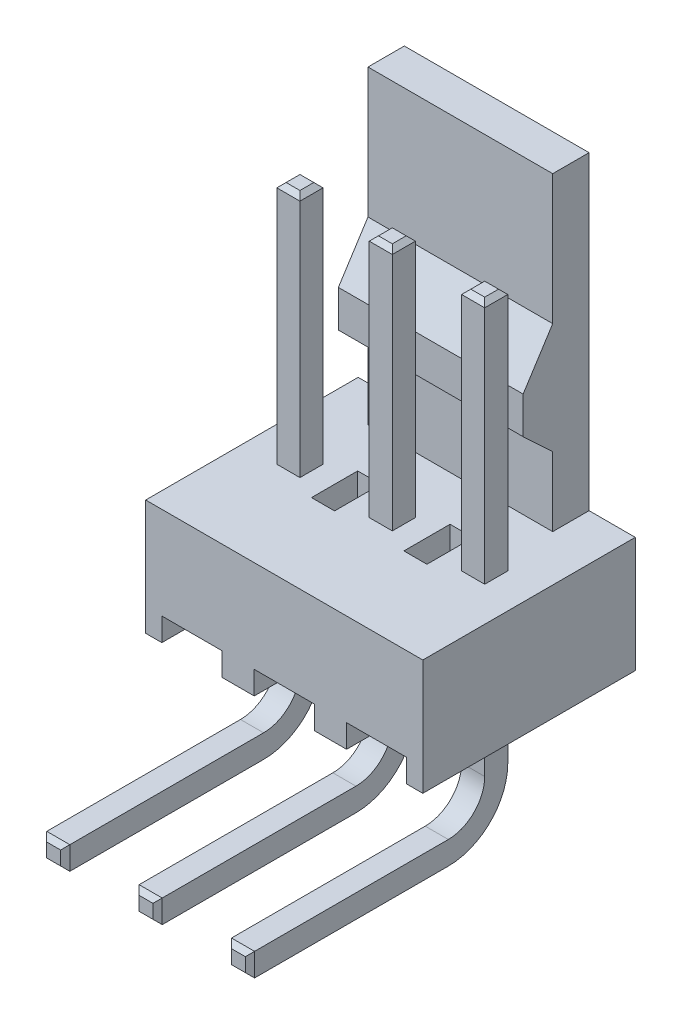
SolidWorks part; units mm, degrees
ref_plane "Front Plane" through (0, 0, 0) normal (0, 0, 1) x (1, 0, 0)
ref_plane "Top Plane" through (0, 0, 0) normal (0, 1, 0) x (1, 0, 0)
ref_plane "Right Plane" through (0, 0, 0) normal (1, 0, 0) x (0, 0, -1)
ref_plane "Plane1" through (0, -1.5875, 0) normal (0, -1, 0) x (1, 0, 0)
sketch "Sketch1" plane through (0, -1.5875, 0) normal (0, -1, 0) x (1, 0, 0)
  line L0 (-3.81, -2.8702) -> (2.54, -2.8702)
  line L1 (2.54, -2.8702) -> (2.54, 2.9718)
  line L2 (2.54, 2.9718) -> (-3.81, 2.9718)
  line L3 (-3.81, 2.9718) -> (-3.81, -2.8702)
extrude "Boss-Extrude1" add sketch "Sketch1" against normal blind 3.175
ref_plane "Plane2" through (2.54, 0, 0) normal (1, 0, 0) x (0, 0, -1)
sketch "Sketch2" plane through (2.54, 0, 0) normal (1, 0, 0) x (0, 0, -1)
  line L0 (0.651, 4.6355) -> (1.8702, 3.4925)
  line L1 (1.8702, 3.4925) -> (1.8702, 1.5875)
  line L2 (1.8702, 1.5875) -> (2.8702, 1.5875)
  line L3 (2.8702, 1.5875) -> (2.8702, 10.1125)
  line L4 (2.8702, 10.1125) -> (1.8702, 10.1125)
  line L5 (1.8702, 10.1125) -> (1.8702, 6.5405)
  line L6 (1.8702, 6.5405) -> (0.651, 4.6355)
extrude "Boss-Extrude2" add sketch "Sketch2" against normal blind 5.08
sketch "Sketch3" plane through (2.54, 0, 0) normal (1, 0, 0) x (0, 0, -1)
  line L0 (-2.9718, 1.5875) -> (2.8702, 1.5875)
  line L1 (2.8702, 1.5875) -> (2.8702, -1.5875)
  line L2 (2.8702, -1.5875) -> (-2.9718, -1.5875)
  line L3 (-2.9718, -1.5875) -> (-2.9718, 1.5875)
extrude "Boss-Extrude3" add sketch "Sketch3" along normal blind 1.27
sketch "Sketch4" plane through (0, 0, -2.8702) normal (0, 0, -1) x (-1, 0, 0)
  line L0 (-0.8255, -1.5875) -> (0.8255, -1.5875)
  line L1 (0.8255, -1.5875) -> (0.8255, -0.9525)
  line L2 (0.8255, -0.9525) -> (-0.8255, -0.9525)
  line L3 (-0.8255, -0.9525) -> (-0.8255, -1.5875)
extrude "Cut-Extrude1" cut sketch "Sketch4" against normal through all
sketch "Sketch5" plane through (0, -0.9525, 0) normal (0, -1, 0) x (1, 0, 0)
  line L0 (0.3175, -0.3175) -> (-0.3175, -0.3175)
  line L1 (-0.3175, -0.3175) -> (-0.3175, 0.3175)
  line L2 (-0.3175, 0.3175) -> (0.3175, 0.3175)
  line L3 (0.3175, 0.3175) -> (0.3175, -0.3175)
extrude "Boss-Extrude4" add sketch "Sketch5" along normal blind 3.6725
sketch "Sketch6" plane through (0, 0, 0.3175) normal (0, 0, 1) x (1, 0, 0)
  line L0 (0.3175, -3.99) -> (0.3175, -4.625)
  line L1 (0.3175, -4.625) -> (-0.3175, -4.625)
  line L2 (-0.3175, -4.625) -> (-0.3175, -3.99)
  line L3 (-0.3175, -3.99) -> (0.3175, -3.99)
extrude "Boss-Extrude5" add sketch "Sketch6" along normal blind 6.4543
sketch "Sketch7" plane through (0, 0, -2.8702) normal (0, 0, -1) x (-1, 0, 0)
  line L0 (1.7145, -1.5875) -> (3.3655, -1.5875)
  line L1 (3.3655, -1.5875) -> (3.3655, -0.9525)
  line L2 (3.3655, -0.9525) -> (1.7145, -0.9525)
  line L3 (1.7145, -0.9525) -> (1.7145, -1.5875)
extrude "Cut-Extrude2" cut sketch "Sketch7" against normal through all
sketch "Sketch8" plane through (0, -0.9525, 0) normal (0, -1, 0) x (1, 0, 0)
  line L0 (-2.2225, -0.3175) -> (-2.8575, -0.3175)
  line L1 (-2.8575, -0.3175) -> (-2.8575, 0.3175)
  line L2 (-2.8575, 0.3175) -> (-2.2225, 0.3175)
  line L3 (-2.2225, 0.3175) -> (-2.2225, -0.3175)
extrude "Boss-Extrude6" add sketch "Sketch8" along normal blind 3.6725
sketch "Sketch9" plane through (0, 0, 0.3175) normal (0, 0, 1) x (1, 0, 0)
  line L0 (-2.2225, -3.99) -> (-2.2225, -4.625)
  line L1 (-2.2225, -4.625) -> (-2.8575, -4.625)
  line L2 (-2.8575, -4.625) -> (-2.8575, -3.99)
  line L3 (-2.8575, -3.99) -> (-2.2225, -3.99)
extrude "Boss-Extrude7" add sketch "Sketch9" along normal blind 6.4543
sketch "Sketch10" plane through (0, 0, -2.8702) normal (0, 0, -1) x (-1, 0, 0)
  line L0 (-3.3655, -1.5875) -> (-1.7145, -1.5875)
  line L1 (-1.7145, -1.5875) -> (-1.7145, -0.9525)
  line L2 (-1.7145, -0.9525) -> (-3.3655, -0.9525)
  line L3 (-3.3655, -0.9525) -> (-3.3655, -1.5875)
extrude "Cut-Extrude3" cut sketch "Sketch10" against normal through all
sketch "Sketch11" plane through (0, -0.9525, 0) normal (0, -1, 0) x (1, 0, 0)
  line L0 (2.8575, -0.3175) -> (2.2225, -0.3175)
  line L1 (2.2225, -0.3175) -> (2.2225, 0.3175)
  line L2 (2.2225, 0.3175) -> (2.8575, 0.3175)
  line L3 (2.8575, 0.3175) -> (2.8575, -0.3175)
extrude "Boss-Extrude8" add sketch "Sketch11" along normal blind 3.6725
sketch "Sketch12" plane through (0, 0, 0.3175) normal (0, 0, 1) x (1, 0, 0)
  line L0 (2.8575, -4.625) -> (2.2225, -4.625)
  line L1 (2.2225, -4.625) -> (2.2225, -3.99)
  line L2 (2.2225, -3.99) -> (2.8575, -3.99)
  line L3 (2.8575, -3.99) -> (2.8575, -4.625)
extrude "Boss-Extrude9" add sketch "Sketch12" along normal blind 6.4543
sketch "Sketch13" plane through (0, 1.5875, 0) normal (0, 1, 0) x (-1, 0, 0)
  line L0 (-2.2225, -0.3175) -> (-2.8575, -0.3175)
  line L1 (-2.8575, -0.3175) -> (-2.8575, 0.3175)
  line L2 (-2.8575, 0.3175) -> (-2.2225, 0.3175)
  line L3 (-2.2225, 0.3175) -> (-2.2225, -0.3175)
extrude "Boss-Extrude10" add sketch "Sketch13" along normal blind 6.71
sketch "Sketch14" plane through (0, 1.5875, 0) normal (0, 1, 0) x (-1, 0, 0)
  line L0 (-0.3175, 0.3175) -> (0.3175, 0.3175)
  line L1 (0.3175, 0.3175) -> (0.3175, -0.3175)
  line L2 (0.3175, -0.3175) -> (-0.3175, -0.3175)
  line L3 (-0.3175, -0.3175) -> (-0.3175, 0.3175)
extrude "Boss-Extrude11" add sketch "Sketch14" along normal blind 6.71
sketch "Sketch15" plane through (0, 1.5875, 0) normal (0, 1, 0) x (-1, 0, 0)
  line L0 (2.8575, 0.3175) -> (2.8575, -0.3175)
  line L1 (2.8575, -0.3175) -> (2.2225, -0.3175)
  line L2 (2.2225, -0.3175) -> (2.2225, 0.3175)
  line L3 (2.2225, 0.3175) -> (2.8575, 0.3175)
extrude "Boss-Extrude12" add sketch "Sketch15" along normal blind 6.71
sketch "Sketch16" plane through (0, 1.5875, 0) normal (0, 1, 0) x (-1, 0, 0)
  line L0 (-1.5875, 0.635) -> (-1.5875, -0.635)
  line L1 (-1.5875, -0.635) -> (-0.9525, -0.635)
  line L2 (-0.9525, -0.635) -> (-0.9525, 0.635)
  line L3 (-0.9525, 0.635) -> (-1.5875, 0.635)
extrude "Cut-Extrude4" cut sketch "Sketch16" against normal blind 1.27
sketch "Sketch17" plane through (0, 1.5875, 0) normal (0, 1, 0) x (-1, 0, 0)
  line L0 (0.9525, 0.635) -> (0.9525, -0.635)
  line L1 (0.9525, -0.635) -> (1.5875, -0.635)
  line L2 (1.5875, -0.635) -> (1.5875, 0.635)
  line L3 (1.5875, 0.635) -> (0.9525, 0.635)
extrude "Cut-Extrude5" cut sketch "Sketch17" against normal blind 1.27
chamfer "Chamfer1" distance 0.127 angle 45 24 edges at (2.54, -3.99, 6.7718) (2.2225, -4.3075, 6.7718) (2.8575, -4.3075, 6.7718) (2.54, -4.625, 6.7718) (-0.3175, -4.3075, 6.7718) (0, -3.99, 6.7718) (0, -4.625, 6.7718) (0.3175, -4.3075, 6.7718) (-2.54, 8.2975, -0.3175) (-2.8575, 8.2975, 0) (-2.2225, 8.2975, 0) (-2.54, 8.2975, 0.3175) (-2.8575, -4.3075, 6.7718) (-2.54, -3.99, 6.7718) (-2.54, -4.625, 6.7718) (-2.2225, -4.3075, 6.7718) (-0.3175, 8.2975, 0) (0, 8.2975, -0.3175) (0, 8.2975, 0.3175) (0.3175, 8.2975, 0) (2.8575, 8.2975, 0) (2.54, 8.2975, 0.3175) (2.54, 8.2975, -0.3175) (2.2225, 8.2975, 0)
chamfer "Chamfer2" distance 0.7539 angle 32.619 1 edges at (0, 4.6355, -0.651)
fillet "Fillet1" radius 1 3 edges at (-2.54, -3.99, 0.3175) (0, -3.99, 0.3175) (2.54, -3.99, 0.3175)
fillet "Fillet2" radius 1.635 3 edges at (2.54, -4.625, -0.3175) (-2.54, -4.625, -0.3175) (0, -4.625, -0.3175)
ref_plane "Plane3" through (0, 0, 2.9718) normal (0, 0, 1) x (1, 0, 0)
sketch "Sketch18" plane through (0, 0, 2.9718) normal (0, 0, 1) x (1, 0, 0)
  line L0 (-2.2225, -4.625) -> (-2.8575, -4.625)
  line L1 (-2.2225, -4.625) -> (-2.8575, -4.625)
  line L2 (-2.8575, -4.625) -> (-2.8575, -3.99)
  line L3 (-2.8575, -4.625) -> (-2.8575, -3.99)
  line L4 (-2.8575, -3.99) -> (-2.2225, -3.99)
  line L5 (-2.8575, -3.99) -> (-2.2225, -3.99)
  line L6 (-2.2225, -3.99) -> (-2.2225, -4.625)
  line L7 (-2.2225, -3.99) -> (-2.2225, -4.625)
  line L8 (0.3175, -3.99) -> (0.3175, -4.625)
  line L9 (0.3175, -3.99) -> (0.3175, -4.625)
  line L10 (0.3175, -4.625) -> (-0.3175, -4.625)
  line L11 (0.3175, -4.625) -> (-0.3175, -4.625)
  line L12 (-0.3175, -3.99) -> (0.3175, -3.99)
  line L13 (-0.3175, -3.99) -> (0.3175, -3.99)
  line L14 (-0.3175, -4.625) -> (-0.3175, -3.99)
  line L15 (-0.3175, -4.625) -> (-0.3175, -3.99)
  line L16 (2.2225, -4.625) -> (2.2225, -3.99)
  line L17 (2.2225, -4.625) -> (2.2225, -3.99)
  line L18 (2.2225, -3.99) -> (2.8575, -3.99)
  line L19 (2.2225, -3.99) -> (2.8575, -3.99)
  line L20 (2.8575, -4.625) -> (2.2225, -4.625)
  line L21 (2.8575, -4.625) -> (2.2225, -4.625)
  line L22 (2.8575, -3.99) -> (2.8575, -4.625)
  line L23 (2.8575, -3.99) -> (2.8575, -4.625)
  line L24 (-2.8575, -3.99) -> (-2.2225, -4.625) construction
  line L25 (-2.2225, -3.99) -> (-2.8575, -4.625) construction
  line L26 (-0.3175, -4.625) -> (0.3175, -3.99) construction
  line L27 (0.3175, -4.625) -> (-0.3175, -3.99) construction
  line L28 (2.2225, -3.99) -> (2.8575, -4.625) construction
  line L29 (2.2225, -4.625) -> (2.8575, -3.99) construction
  circle A0 centre (-2.54, -4.3075) radius 0.449
  circle A1 centre (0, -4.3075) radius 0.449
  circle A2 centre (2.54, -4.3075) radius 0.449
